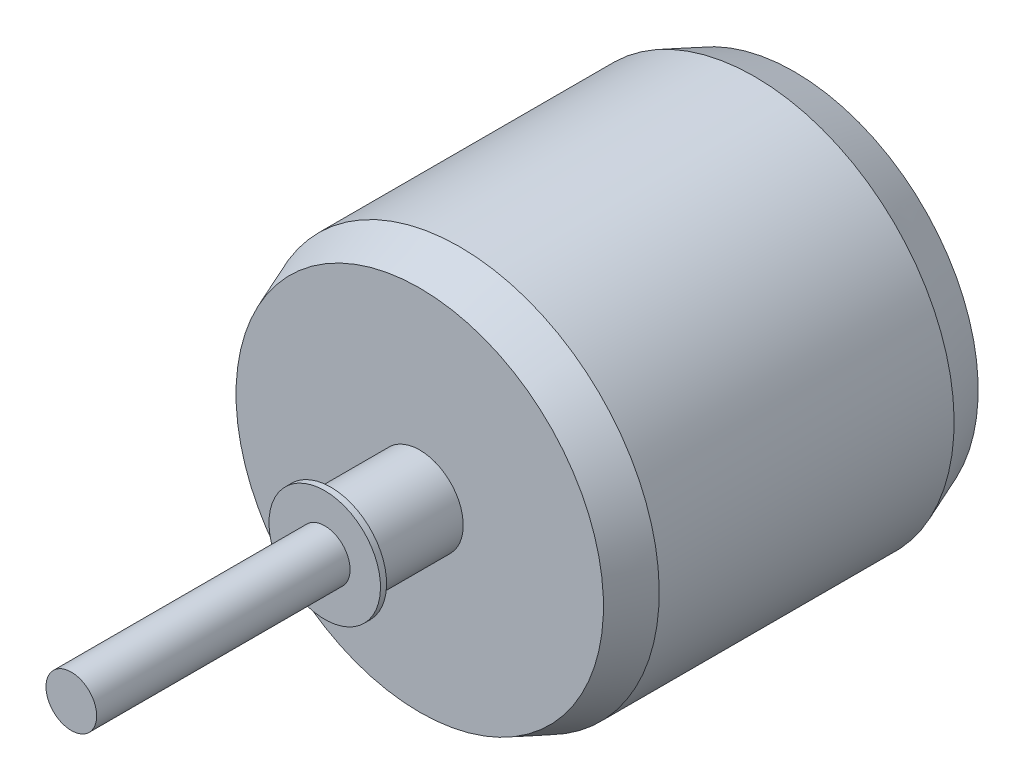
SolidWorks part; units mm, degrees
ref_plane "Front Plane" through (0, 0, 0) normal (0, 0, 1) x (1, 0, 0)
ref_plane "Top Plane" through (0, 0, 0) normal (0, 1, 0) x (1, 0, 0)
ref_plane "Right Plane" through (0, 0, 0) normal (1, 0, 0) x (0, 0, -1)
sketch "Sketch1" plane through (0, 0, 0) normal (1, 0, 0) x (0, 0, -1)
  line L0 (58.65, 0) -> (-58.65, 0)
  line L1 (93.1145, 0) -> (-93.1145, 0) construction
  line L4 (-58.65, 0) -> (-58.65, 4)
  line L5 (-58.65, 4) -> (-18.65, 4)
  line L6 (-18.65, 4) -> (-18.65, 8.8)
  line L9 (-3.65, 6.8605) -> (-16.7451, 6.8605)
  line L10 (-16.7451, 6.8605) -> (-17.6846, 8.8)
  line L12 (-17.6846, 8.8) -> (-18.65, 8.8)
  line L14 (-3.65, 6.8605) -> (-3.65, 29)
  line L15 (2.65, 31.5) -> (49.2, 31.5)
  line L16 (58.65, 7) -> (58.65, 0)
  line L19 (2.65, 31.5) -> (-3.65, 29)
  line L21 (58.65, 7) -> (55.5, 7)
  line L23 (55.5, 7) -> (55.5, 29)
  line L26 (55.5, 29) -> (49.2, 31.5)
  point P3 (0, 0)
  point P8 (0, 0)
revolve "Revolve2" add sketch "Sketch1" angle 360 about L1
